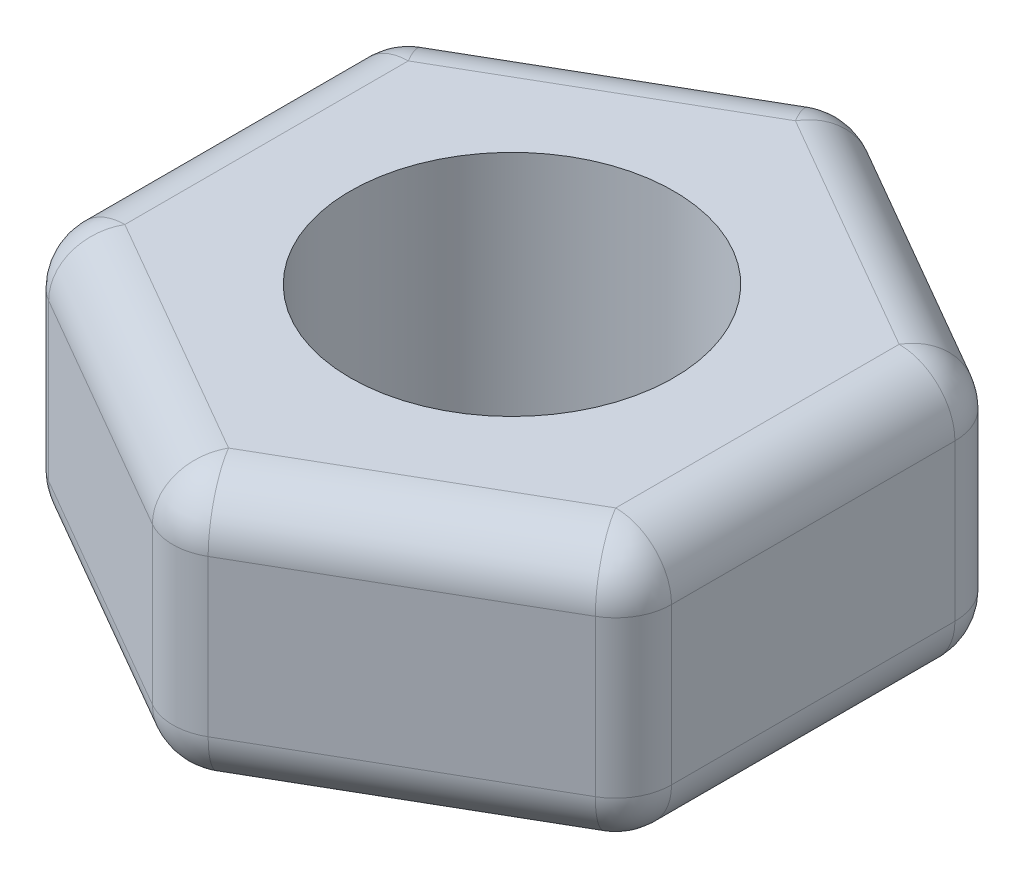
SolidWorks part; units mm, degrees
material "AISI 1020"
ref_plane "Front Plane" through (0, 0, 0) normal (0, 0, 1) x (1, 0, 0)
ref_plane "Top Plane" through (0, 0, 0) normal (0, 1, 0) x (1, 0, 0)
ref_plane "Right Plane" through (0, 0, 0) normal (1, 0, 0) x (0, 0, -1)
sketch "Sketch1" plane through (0, 0, 0) normal (0, 1, 0) x (1, 0, 0)
  line L1 (0, 3.1177) -> (-2.7, 1.5588)
  line L2 (-2.7, 1.5588) -> (-2.7, -1.5588)
  line L3 (-2.7, -1.5588) -> (0, -3.1177)
  line L4 (0, -3.1177) -> (2.7, -1.5588)
  line L5 (2.7, -1.5588) -> (2.7, 1.5588)
  line L6 (2.7, 1.5588) -> (0, 3.1177)
  circle A0 centre (0, 0) radius 2.7 construction
  circle A1 centre (0, 0) radius 1.45
  dimension "D2" = 2.9
  dimension "D1" = 5.4
extrude "Boss-Extrude1" add sketch "Sketch1" along normal blind 2.4
fillet "Fillet1" radius 0.5 18 edges at (-1.35, 0, -2.3383) (-2.7, 0, 0) (-1.35, 0, 2.3383) (1.35, 0, 2.3383) (1.35, 0, -2.3383) (2.7, 0, 0) (2.7, 2.4, 0) (-1.35, 2.4, 2.3383) (-2.7, 2.4, 0) (-1.35, 2.4, -2.3383) (1.35, 2.4, -2.3383) (1.35, 2.4, 2.3383) (2.7, 1.2, -1.5588) (-2.7, 1.2, 1.5588) (-2.7, 1.2, -1.5588) (0, 1.2, -3.1177) (2.7, 1.2, 1.5588) (0, 1.2, 3.1177)
